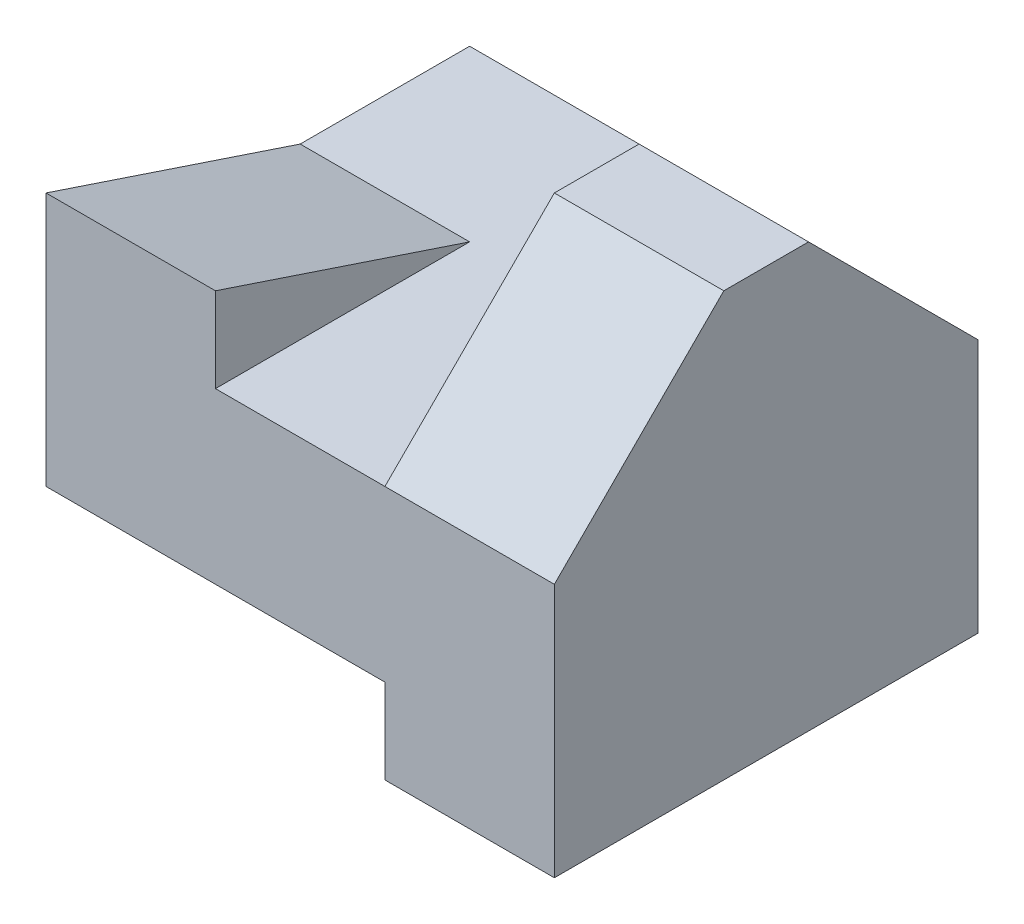
SolidWorks part; units mm, degrees
ref_plane "Front Plane" through (0, 0, 0) normal (0, 0, 1) x (1, 0, 0)
ref_plane "Top Plane" through (0, 0, 0) normal (0, 1, 0) x (1, 0, 0)
ref_plane "Right Plane" through (0, 0, 0) normal (1, 0, 0) x (0, 0, -1)
sketch "Sketch1" plane through (0, 0, 0) normal (0, 0, 1) x (1, 0, 0)
  line L1 (0, 0) -> (30, 0)
  line L2 (0, 0) -> (0, 25)
  line L3 (0, 25) -> (30, 25)
  line L4 (30, 0) -> (30, 25)
  dimension "D1" = 30
  dimension "D2" = 25
extrude "Boss-Extrude1" add sketch "Sketch1" along normal blind 25
sketch "Sketch2" plane through (30, 0, 0) normal (1, 0, 0) x (0, 0, -1)
  line L0 (-25, 25) -> (-25, 15)
  line L1 (-25, 0) -> (-25, 25) construction
  line L2 (-25, 15) -> (-15, 25)
  line L3 (-25, 25) -> (0, 25) construction
  line L4 (-15, 25) -> (-25, 25)
  line L5 (-10, 25) -> (0, 25)
  line L6 (0, 25) -> (0, 15)
  line L7 (0, 0) -> (0, 25) construction
  line L8 (0, 15) -> (-10, 25)
  dimension "D1" = 10
  dimension "D2" = 10
  dimension "D3" = 10
  dimension "D4" = 10
extrude "Cut-Extrude1" cut sketch "Sketch2" against normal blind 10
sketch "Sketch3" plane through (0, 0, 25) normal (0, 0, 1) x (1, 0, 0)
  line L0 (0, 0) -> (30, 0) construction
  line L1 (10, 0) -> (20, 0)
  line L2 (10, 0) -> (10, 5)
  line L3 (10, 5) -> (20, 5)
  line L4 (20, 0) -> (20, 5)
  line L5 (30, 0) -> (30, 15) construction
  dimension "D1" = 5
  dimension "D2" = 10
  dimension "D3" = 10
extrude "Cut-Extrude2" cut sketch "Sketch3" against normal blind 30
sketch "Sketch4" plane through (0, 0, 25) normal (0, 0, 1) x (1, 0, 0)
  line L0 (0, 25) -> (20, 25)
  line L1 (20, 25) -> (20, 15)
  line L2 (20, 15) -> (10, 15)
  line L3 (10, 15) -> (10, 20)
  line L4 (10, 20) -> (0, 20)
  line L5 (0, 25) -> (0, 0) construction
  line L6 (0, 20) -> (0, 25)
  dimension "D1" = 5
  dimension "D2" = 10
extrude "Cut-Extrude3" cut sketch "Sketch4" against normal blind 30
sketch "Sketch6" plane through (0, 0, 0) normal (-1, 0, 0) x (0, 0, 1)
  line L0 (25, 20) -> (10, 15)
  line L1 (25, 20) -> (25, 0) construction
  line L2 (10, 15) -> (10, 20)
  line L3 (0, 20) -> (25, 20) construction
  line L4 (10, 20) -> (25, 20)
  line L5 (25, 0) -> (10, 0)
  line L6 (25, 0) -> (0, 0) construction
  line L7 (10, 0) -> (25, 5)
  line L8 (25, 5) -> (25, 0)
  dimension "D1" = 5
  dimension "D2" = 5
  dimension "D3" = 15
extrude "Cut-Extrude5" cut sketch "Sketch6" against normal blind 10
sketch "Sketch7" plane through (0, 20, 0) normal (0, 1, 0) x (1, 0, 0)
  line L1 (0, -10) -> (10, -10)
  line L2 (0, -10) -> (0, 0)
  line L3 (0, 0) -> (10, 0)
  line L4 (10, -10) -> (10, 0)
extrude "Cut-Extrude6" cut sketch "Sketch7" against normal blind 5
